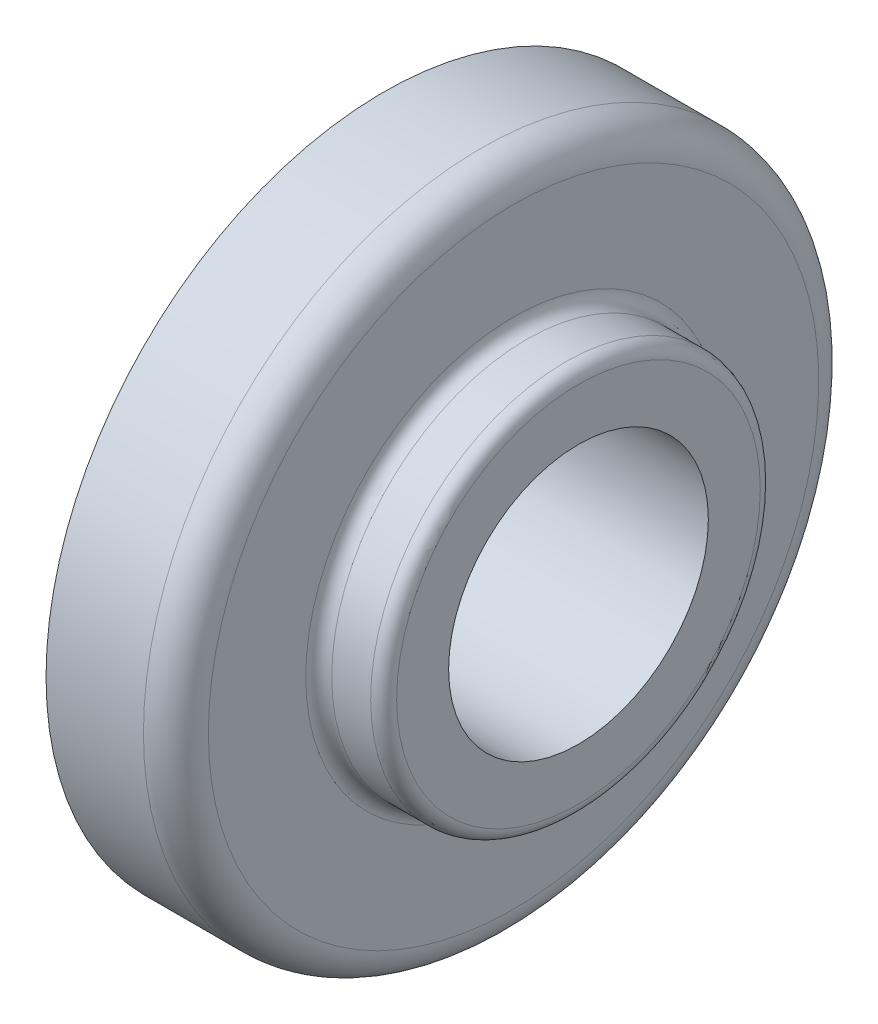
SolidWorks part; units mm, degrees
ref_plane "Front Plane" through (0, 0, 0) normal (0, 0, 1) x (1, 0, 0)
ref_plane "Top Plane" through (0, 0, 0) normal (0, 1, 0) x (1, 0, 0)
ref_plane "Right Plane" through (0, 0, 0) normal (1, 0, 0) x (0, 0, -1)
sketch "Sketch1" plane through (0, 0, 0) normal (0, 1, 0) x (1, 0, 0)
  line L1 (-2.8182, -7.3273) -> (1.1059, -7.3273)
  line L2 (-2.8182, -7.3273) -> (-2.8182, 18.6727)
  line L3 (-2.8182, 18.6727) -> (4.6818, 18.6727)
  line L4 (7.1818, 8.6727) -> (7.1818, 16.1727)
  line L5 (-2.8182, -7.3273) -> (7.1818, 18.6727) construction
  line L6 (-2.8182, 18.6727) -> (1.1059, -7.3273) construction
  line L7 (1.1059, -7.3273) -> (12.1818, -7.3273)
  line L9 (8.1818, 7.6727) -> (11.1818, 7.6727)
  line L10 (12.1818, -7.3273) -> (12.1818, 6.6727)
  arc A0 (4.6818, 18.6727) -> (7.1818, 16.1727) centre (4.6818, 16.1727) cw
  arc A1 (7.1818, 8.6727) -> (8.1818, 7.6727) centre (8.1818, 8.6727) ccw
  arc A2 (11.1818, 7.6727) -> (12.1818, 6.6727) centre (11.1818, 6.6727) cw
  point P0 (0, 0)
  point P14 (7.1818, 7.6727)
  point P17 (12.1818, 7.6727)
  dimension "D5" = 2.5
  dimension "D6" = 1
  dimension "D1" = 26
  dimension "D2" = 10
  dimension "D3" = 5
  dimension "D4" = 15
revolve "Revolve1" add sketch "Sketch1" angle 360 about L1
sketch "Sketch2" plane through (12.1818, 0, 0) normal (1, 0, 0) x (0, 0, -1)
  circle A0 centre (-7.3273, 0) radius 10
  dimension "D1" = 20
extrude "Extrude1" cut sketch "Sketch2" against normal through all
